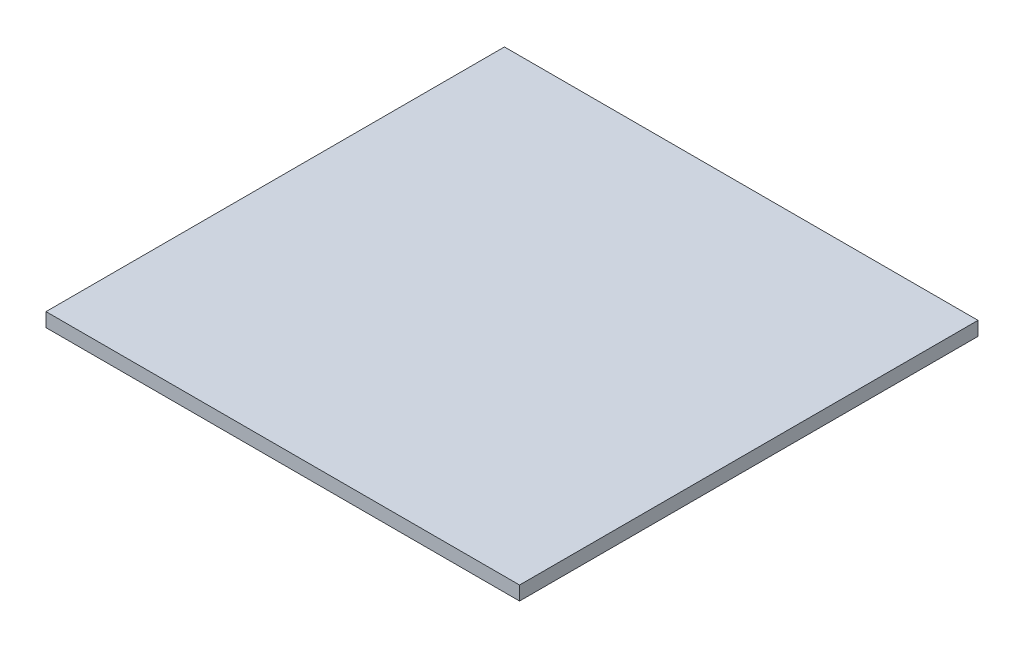
SolidWorks part; units mm, degrees
ref_plane "Front Plane" through (0, 0, 0) normal (0, 0, 1) x (1, 0, 0)
ref_plane "Top Plane" through (0, 0, 0) normal (0, 1, 0) x (1, 0, 0)
ref_plane "Right Plane" through (0, 0, 0) normal (1, 0, 0) x (0, 0, -1)
sketch "Sketch1" plane through (0, 0, 0) normal (0, 1, 0) x (1, 0, 0)
  line L1 (-44.2815, 20.698) -> (57.7785, 20.698)
  line L2 (-44.2815, 20.698) -> (-44.2815, -78.102)
  line L3 (-44.2815, -78.102) -> (57.7785, -78.102)
  line L4 (57.7785, 20.698) -> (57.7785, -78.102)
  dimension "D1" = 102.06
  dimension "D2" = 98.8
extrude "Boss-Extrude1" add sketch "Sketch1" along normal blind 3
equation "\"Fit\"= 1"
equation "\"cover width\"= 98.8"
equation "\"bottom 4 length\"= 102.06"
equation "\"thinner acrylic\" = 3"
equation "\"D1@Sketch1\"=\"bottom 4 length\""
equation "\"D2@Sketch1\"=\"cover width\""
equation "\"D1@Boss-Extrude1\"=\"thinner acrylic\""
